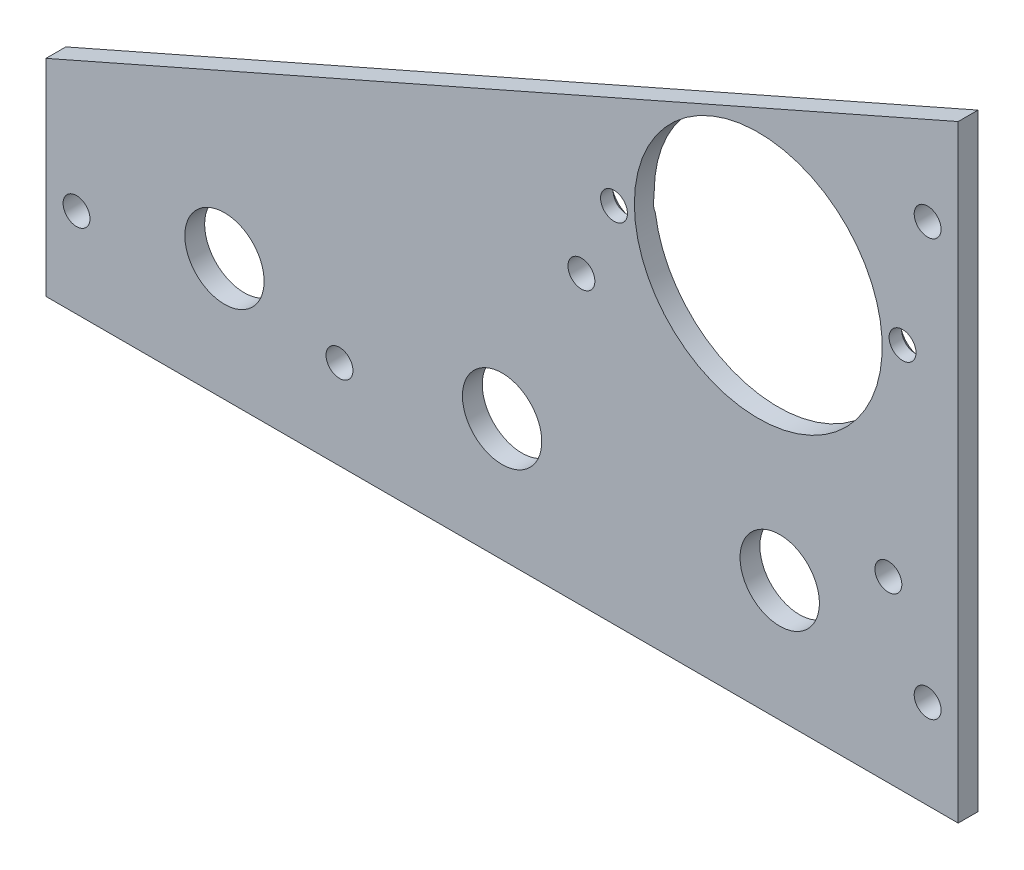
SolidWorks part; units mm, degrees
ref_plane "Front Plane" through (0, 0, 0) normal (0, 0, 1) x (1, 0, 0)
ref_plane "Top Plane" through (0, 0, 0) normal (0, 1, 0) x (1, 0, 0)
ref_plane "Right Plane" through (0, 0, 0) normal (1, 0, 0) x (0, 0, -1)
sketch "Sketch1" plane through (0, 0, 0) normal (0, 0, 1) x (1, 0, 0)
  line L4 (0, 97.282) -> (-146.05, 33.02)
  line L5 (-146.05, 33.02) -> (-146.05, 0)
  line L6 (-146.05, 0) -> (0, 0)
  line L7 (0, 0) -> (0, 97.282)
  line L8 (0, 97.282) -> (-146.05, 33.02)
  line L9 (-146.05, 33.02) -> (-146.05, 0)
  line L10 (-146.05, 0) -> (0, 0)
  line L11 (0, 0) -> (0, 97.282)
  dimension "D1" = 0
extrude "Boss-Extrude1" add sketch "Sketch1" against normal blind 3.175
hole_wizard "#6 Clearance Hole1" positions "Sketch6" profile "Sketch5" hole size "#6" standard "ANSI Inch" end condition through all
sketch "Sketch6" plane through (0, 0, -3.175) normal (0, 0, -1) x (-1, 0, 0)
  point P1 (4.8895, 80.9625)
  point P4 (4.8895, 14.2875)
  point P7 (141.1605, 14.2875)
  point P10 (11.176, 28.575)
  point P12 (60.325, 46.0375)
  point P14 (99.06, 14.2875)
sketch "Sketch5" plane through (-4.8895, 80.9625, -3.175) normal (1, 0, 0) x (0, 1, 0)
  line L0 (0, 0) -> (0, 3.175)
  line L1 (0, 3.175) -> (2.1526, 3.175)
  line L2 (2.1526, 3.175) -> (2.1526, 0)
  line L5 (2.1526, 0) -> (0, 0)
  line L11 (0, -6.35) -> (0, 107.95) construction
  dimension "Thru Hole Dia." = 4.3053
  dimension "Thru Hole Depth" = 3.175
sketch "Sketch7" plane through (0, 0, -3.175) normal (0, 0, -1) x (-1, 0, 0)
  circle A0 centre (32.004, 59.944) radius 19.8438 construction
  circle A1 centre (32.004, 59.944) radius 19.8438
  circle A2 centre (28.575, 19.3759) radius 6.35
  circle A3 centre (73.025, 19.558) radius 6.35
  circle A4 centre (117.475, 19.558) radius 6.35
  ellipse E0 centre (28.575, 21.3285) end of major axis (30.575, 21.3285) minor radius 1.9526 construction
  dimension "D1" = 12.7
extrude "Cut-Extrude1" cut sketch "Sketch7" against normal through all
hole_wizard "CSK for #6 Flat Head Machine Screw (100)1" positions "Sketch8" profile "Sketch9" countersink size "#6" standard "ANSI Inch" end condition up to next
sketch "Sketch8" plane through (0, 0, -3.175) normal (0, 0, -1) x (-1, 0, 0)
  point P0 (8.904, 61.8383)
  point P2 (55.104, 58.0497)
sketch "Sketch9" plane through (-8.904, 61.8383, -3.175) normal (1, 0, 0) x (0, 1, 0)
  line L0 (0, 0) -> (0, 3.175)
  line L1 (0, 3.175) -> (2.1526, 3.175)
  line L2 (2.1526, 3.175) -> (2.1526, 1.1669)
  line L3 (2.1526, 1.1669) -> (3.5433, 0)
  line L5 (3.5433, 0) -> (0, 0)
  line L6 (-2.1526, 1.1669) -> (-3.5433, 0) construction
  line L11 (0, -6.35) -> (0, 107.95) construction
  dimension "Thru Hole Dia." = 4.3053
  dimension "Thru Hole Depth" = 3.175
  dimension "Near C'Sink Dia." = 7.0866
  dimension "Near C'Sink Angle" = 100
